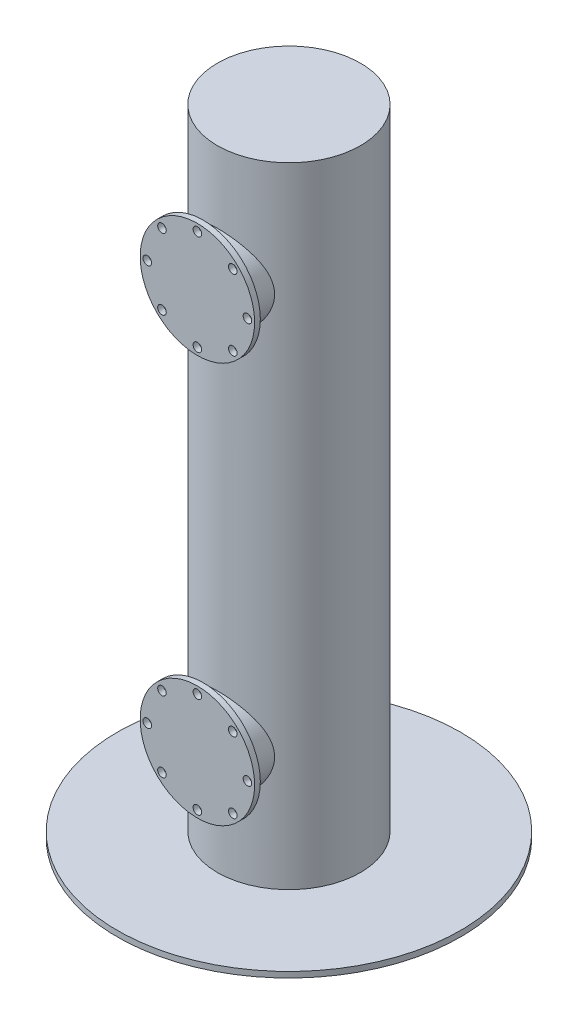
SolidWorks part; units mm, degrees
material "Plain Carbon Steel"
ref_plane "Front Plane" through (0, 0, 0) normal (0, 0, 1) x (1, 0, 0)
ref_plane "Top Plane" through (0, 0, 0) normal (0, 1, 0) x (1, 0, 0)
ref_plane "Right Plane" through (0, 0, 0) normal (1, 0, 0) x (0, 0, -1)
sketch "Sketch1" plane through (0, 0, 0) normal (0, 1, 0) x (1, 0, 0)
  circle A0 centre (0, 0) radius 25
  dimension "D1" = 50
extrude "Boss-Extrude1" add sketch "Sketch1" along normal blind 220
sketch "Sketch2" plane through (0, 0, 0) normal (0, 0, 1) x (1, 0, 0)
  circle A0 centre (0, 180) radius 15
  circle A1 centre (0, 40) radius 15
  dimension "D1" = 30
  dimension "D2" = 30
  dimension "D6" = 180
  dimension "D3" = 180
  dimension "D4" = 40
  dimension "D5" = 140
extrude "Boss-Extrude2" add sketch "Sketch2" along normal blind 30
sketch "Sketch3" plane through (0, 0, 30) normal (0, 0, 1) x (1, 0, 0)
  circle A0 centre (0, 180) radius 20
  circle A2 centre (0, 197.5) radius 1.5
  circle A3 centre (12.3744, 192.3744) radius 1.5
  circle A4 centre (17.5, 180) radius 1.5
  circle A5 centre (12.3744, 167.6256) radius 1.5
  circle A6 centre (0, 162.5) radius 1.5
  circle A7 centre (-12.3744, 167.6256) radius 1.5
  circle A8 centre (-17.5, 180) radius 1.5
  circle A9 centre (-12.3744, 192.3744) radius 1.5
  circle A10 centre (0, 40) radius 20
  circle A11 centre (0, 57.5) radius 1.5
  circle A12 centre (12.3744, 52.3744) radius 1.5
  circle A13 centre (17.5, 40) radius 1.5
  circle A14 centre (12.3744, 27.6256) radius 1.5
  circle A15 centre (0, 22.5) radius 1.5
  circle A16 centre (-12.3744, 27.6256) radius 1.5
  circle A17 centre (-17.5, 40) radius 1.5
  circle A18 centre (-12.3744, 52.3744) radius 1.5
  point P24 (0, 180)
  point P43 (0, 40)
  dimension "D1" = 40
  dimension "D2" = 0
  dimension "D3" = 3
  dimension "D4" = 17.5
  dimension "D5" = 17.5
  dimension "D7" = 0
  dimension "D6" = 2
extrude "Boss-Extrude4" add sketch "Sketch3" along normal blind 2
sketch "Sketch4" plane through (0, 0, 0) normal (0, -1, 0) x (1, 0, 0)
  circle A0 centre (0, 0) radius 60
  dimension "D1" = 120
extrude "Boss-Extrude5" add sketch "Sketch4" along normal blind 2
